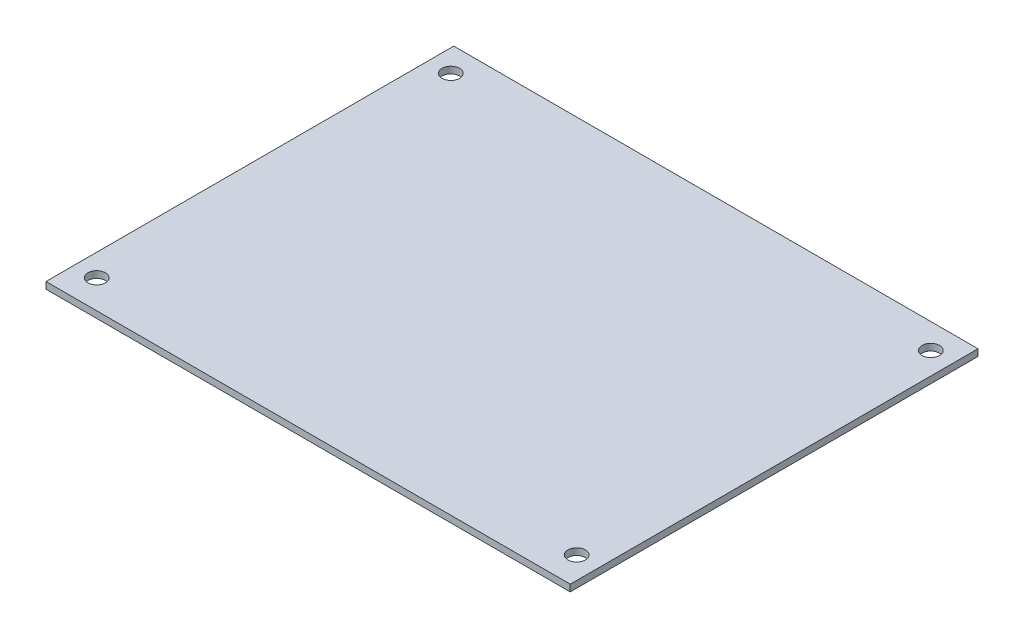
SolidWorks part; units mm, degrees
ref_plane "前基準面" through (0, 0, 0) normal (0, 0, 1) x (1, 0, 0)
ref_plane "上基準面" through (0, 0, 0) normal (0, 1, 0) x (1, 0, 0)
ref_plane "右基準面" through (0, 0, 0) normal (1, 0, 0) x (0, 0, -1)
sketch "草圖1" plane through (0, 0, 0) normal (0, 1, 0) x (1, 0, 0)
  line L1 (-45, 35) -> (45, 35)
  line L2 (-45, 35) -> (-45, -35)
  line L3 (-45, -35) -> (45, -35)
  line L4 (45, 35) -> (45, -35)
  line L5 (-45, 35) -> (45, -35) construction
  line L6 (-45, -35) -> (45, 35) construction
  point P0 (0, 0)
  dimension "D1" = 90
  dimension "D2" = 70
extrude "填料-伸長1" add sketch "草圖1" along normal blind 1.15
sketch "草圖2" plane through (0, 1.15, 0) normal (0, 1, 0) x (1, 0, 0)
  line L0 (45, 35) -> (-45, 35) construction
  line L1 (45, -35) -> (45, 35) construction
  line L2 (0, 35) -> (0, -35) construction
  line L3 (-45, -35) -> (45, -35) construction
  circle A0 centre (41.2, 30.7) radius 1.5
  circle A1 centre (41.2, -30.1) radius 1.5
  circle A2 centre (-41.2, -30.1) radius 1.5
  circle A3 centre (-41.2, 30.7) radius 1.5
  dimension "D3" = 3
  dimension "D1" = 4.3
  dimension "D2" = 3.8
  dimension "D4" = 4.9
extrude "除料-伸長1" cut sketch "草圖2" against normal through all
sketch "草圖3" plane through (0, 1.15, 0) normal (0, 1, 0) x (1, 0, 0)
  text T0 "UP"
